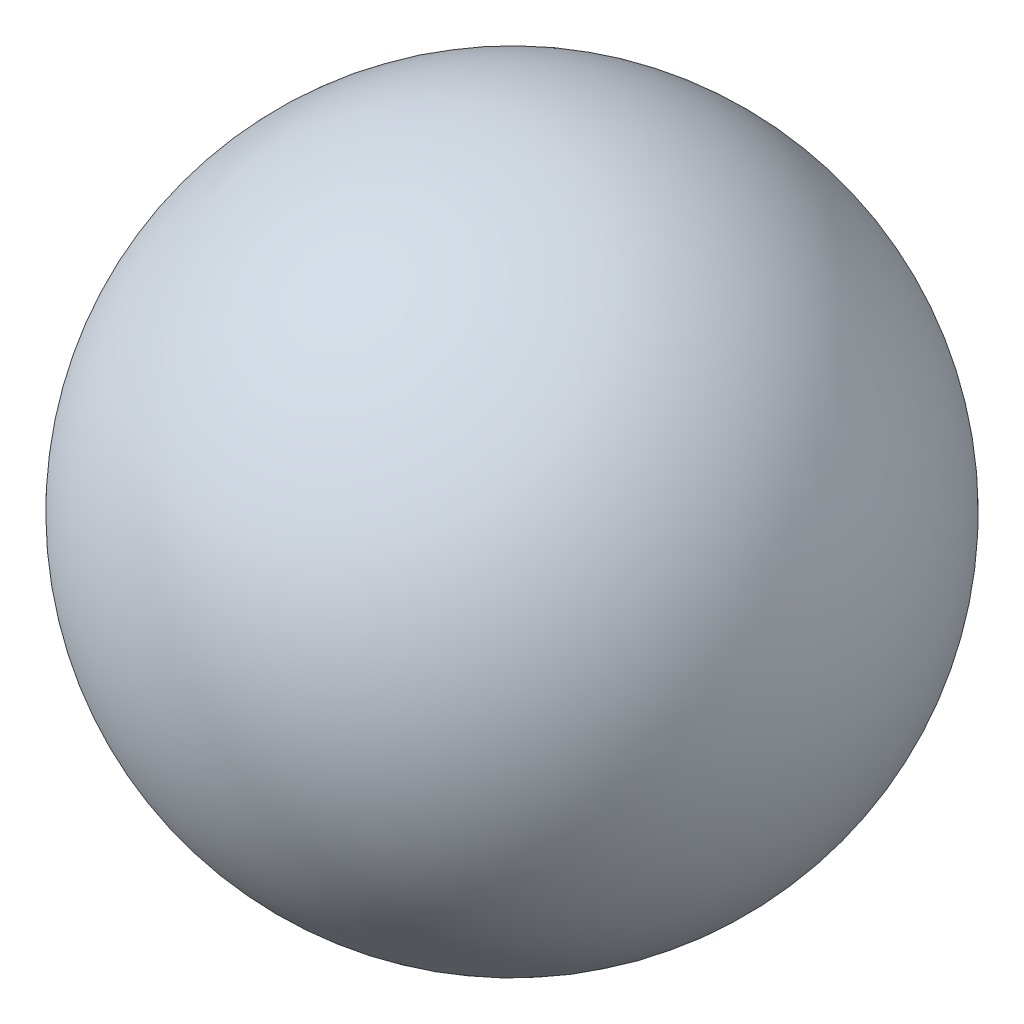
SolidWorks part; units mm, degrees
ref_plane "Front Plane" through (0, 0, 0) normal (0, 0, 1) x (1, 0, 0)
ref_plane "Top Plane" through (0, 0, 0) normal (0, 1, 0) x (1, 0, 0)
ref_plane "Right Plane" through (0, 0, 0) normal (1, 0, 0) x (0, 0, -1)
sketch "Sketch1" plane through (0, 0, 0) normal (0, 1, 0) x (1, 0, 0)
  line L0 (-227.2691, -112.4997) -> (-105.6127, 17.1635) construction
  line L1 (-105.6127, 17.1635) -> (-227.2691, -112.4997)
  arc A0 (-105.6127, 17.1635) -> (-227.2691, -112.4997) centre (-166.4409, -47.6681) ccw
  dimension "D1" = 88.9
revolve "Revolve4" add sketch "Sketch1" angle 360 about L0
